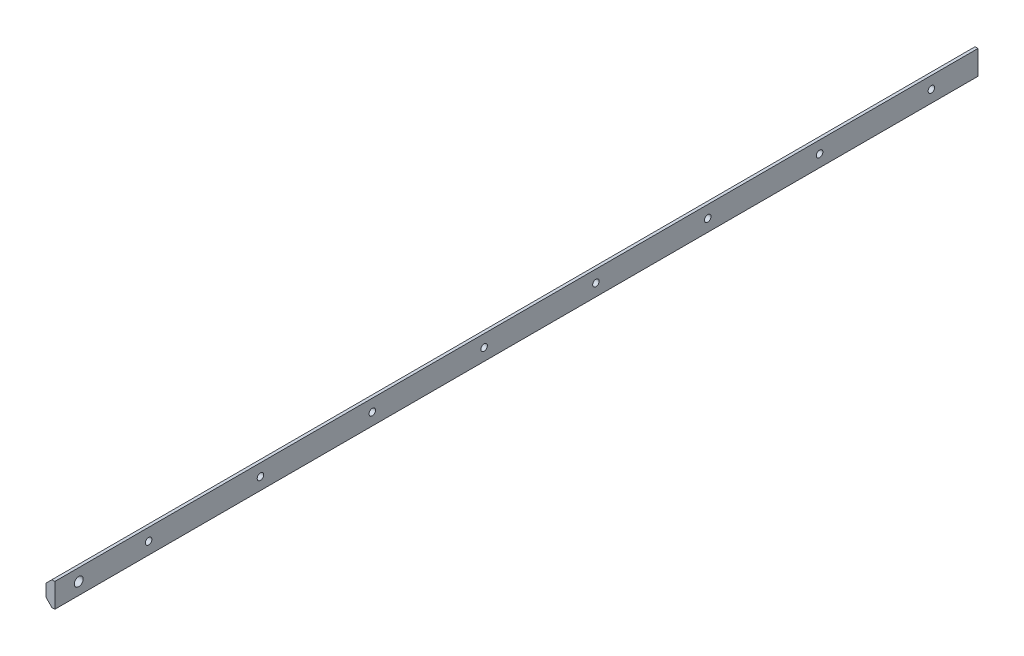
SolidWorks part; units mm, degrees
material "1023 Carbon Steel Sheet (SS)"
ref_plane "Front Plane" through (0, 0, 0) normal (0, 0, 1) x (1, 0, 0)
ref_plane "Top Plane" through (0, 0, 0) normal (0, 1, 0) x (1, 0, 0)
ref_plane "Right Plane" through (0, 0, 0) normal (1, 0, 0) x (0, 0, -1)
sketch "Sketch1" plane through (0, 0, 0) normal (0, 0, -1) x (-1, 0, 0)
  line L15 (-223.5886, 192.9841) -> (-218.8261, 192.9841)
  line L16 (-223.5886, 192.9841) -> (-223.5886, 180.0345)
  line L17 (-223.5886, 180.0345) -> (-218.8261, 180.0345)
  line L18 (-218.8261, 192.9841) -> (-218.8261, 180.0345)
  dimension "D1" = 4.7625
extrude "Boss-Extrude1" add sketch "Sketch1" along normal up to vertex (495.2982 mm away)
sketch "Sketch9" plane through (0, 0, 0) normal (0, 0, 1) x (1, 0, 0)
  line L0 (223.5886, 192.9841) -> (223.5886, 180.0345) construction
  line L1 (223.5886, 182.2218) -> (223.5886, 186.5093)
  line L2 (223.5886, 186.5093) -> (223.5886, 190.7968)
  line B0 (225.7984, 181.1922) -> (225.7984, 182.2218)
  line B1 (223.5886, 182.2218) -> (223.5886, 180.1072)
  line B2 (217.6069, 184.9161) -> (217.6069, 188.1025)
  line B3 (218.5394, 190.3501) -> (221.8355, 193.6387)
  line B4 (223.5886, 192.9114) -> (223.5886, 190.7968)
  line B5 (225.7984, 192.8424) -> (225.7984, 196.0597)
  line B6 (220.3054, 195.2337) -> (216.9967, 191.9325)
  line B7 (214.7542, 191.0051) -> (211.4426, 191.0051)
  line B8 (208.8109, 199.2093) -> (207.7813, 199.2093)
  line B9 (202.6082, 190.7968) -> (202.6082, 192.9114)
  line B10 (204.3613, 193.6387) -> (207.6574, 190.3501)
  line B11 (208.5899, 188.1025) -> (208.5899, 184.9161)
  line B12 (200.3984, 180.1762) -> (200.3984, 176.9589)
  circle B13 centre (213.0984, 186.5093) radius 2.6035
  arc B14 (211.3891, 182.0135) -> (209.1461, 181.0856) centre (211.3891, 178.8385) ccw
  arc B15 (224.6376, 183.2708) -> (223.5886, 182.2218) centre (224.6376, 182.2218) ccw
  arc B16 (218.5394, 190.3501) -> (217.6069, 188.1025) centre (220.7819, 188.1025) ccw
  arc B17 (223.5886, 192.9114) -> (221.8355, 193.6387) centre (222.5612, 192.9114) ccw
  arc B18 (224.7494, 189.7477) -> (225.7984, 190.7968) centre (224.7494, 190.7968) ccw
  arc B19 (225.7982, 197.0757) -> (223.6648, 199.2091) centre (223.6902, 197.1011) ccw
  arc B20 (216.3369, 198.0485) -> (217.3859, 196.9995) centre (217.3859, 198.0485) ccw
  arc B21 (220.3054, 195.2337) -> (219.5752, 196.9995) centre (219.5752, 195.9656) ccw
  arc B22 (206.7653, 199.2093) -> (207.7813, 199.2093) centre (207.2733, 199.2093) ccw
  arc B23 (207.6574, 182.6685) -> (208.5899, 184.9161) centre (205.4149, 184.9161) ccw
  arc B24 (202.6082, 182.2218) -> (201.5592, 183.2708) centre (201.5592, 182.2218) ccw
  arc B25 (201.4474, 183.2708) -> (200.3984, 182.2218) centre (201.4474, 182.2218) ccw
sketch_block_instance "Block-8020 1x1-1"
sketch_block "Block-8020 1x1"
hole_wizard "1/4 (0.1875) Diameter Hole1" positions "Sketch4" profile "Sketch5" hole size "1/4" standard "ANSI Inch" end condition up to next
sketch "Sketch4" plane through (223.5886, 0, 0) normal (1, 0, 0) x (0, 0, -1)
  point P0 (12.7982, 186.5093)
sketch "Sketch5" plane through (223.5886, 186.5093, -12.7982) normal (0, 1, 0) x (0, 0, -1)
  line L0 (0, 0) -> (0, 4.7625)
  line L1 (0, 4.7625) -> (2.3812, 4.7625)
  line L2 (2.3812, 4.7625) -> (2.3812, 0)
  line L5 (2.3812, 0) -> (0, 0)
  line L11 (0, -6.35) -> (0, 107.95) construction
  dimension "Thru Hole Dia." = 4.7625
  dimension "Thru Hole Depth" = 4.7625
chamfer "Chamfer1" distance 3.175 angle 45 2 edges at (218.8261, 192.9841, -247.6491) (218.8261, 180.0345, -247.6491)
hole_wizard "Ø3.0mm Dowel Hole1" positions "Sketch6" profile "Sketch8" hole size "Ø3.0" standard "ANSI Metric" end condition up to next
sketch "Sketch6" plane through (223.5886, 0, 0) normal (1, 0, 0) x (0, 0, -1)
  point P0 (470.2982, 186.5093)
  point P3 (410.2982, 186.5093)
  point P6 (350.2982, 186.5093)
  point P9 (290.2982, 186.5093)
  point P15 (170.2982, 186.5093)
  point P18 (110.2982, 186.5093)
  point P21 (50.2982, 186.5093)
  point P26 (230.2982, 186.5093)
sketch "Sketch8" plane through (223.5886, 186.5093, -470.2982) normal (0, 1, 0) x (0, 0, -1)
  line L0 (0, 0) -> (0, 4.7625)
  line L1 (0, 4.7625) -> (1.75, 4.7625)
  line L2 (1.75, 4.7625) -> (1.75, 0)
  line L5 (1.75, 0) -> (0, 0)
  line L11 (0, -6.35) -> (0, 107.95) construction
  dimension "Thru Hole Dia." = 3.5
  dimension "Thru Hole Depth" = 4.7625
sketch "Sketch10" plane through (223.5886, 0, 0) normal (1, 0, 0) x (0, 0, -1)
  line L0 (0, 192.9841) -> (140.2982, 192.9841) construction
  line L1 (495.2982, 192.9841) -> (0, 192.9841) construction
  line L2 (140.2982, 192.9841) -> (320.2982, 192.9841) construction
  line L3 (320.2982, 192.9841) -> (495.2982, 192.9841) construction
  line L4 (110.2982, 186.5093) -> (170.2982, 186.5093) construction
  line L5 (140.2982, 192.9841) -> (140.2982, 123.3602) construction
  line L6 (290.2982, 186.5093) -> (350.2982, 186.5093) construction
  line L8 (320.2982, 123.3602) -> (320.2982, 192.9841) construction
  point P17 (320.2982, 186.5093)
  point P19 (140.2982, 186.5093)
